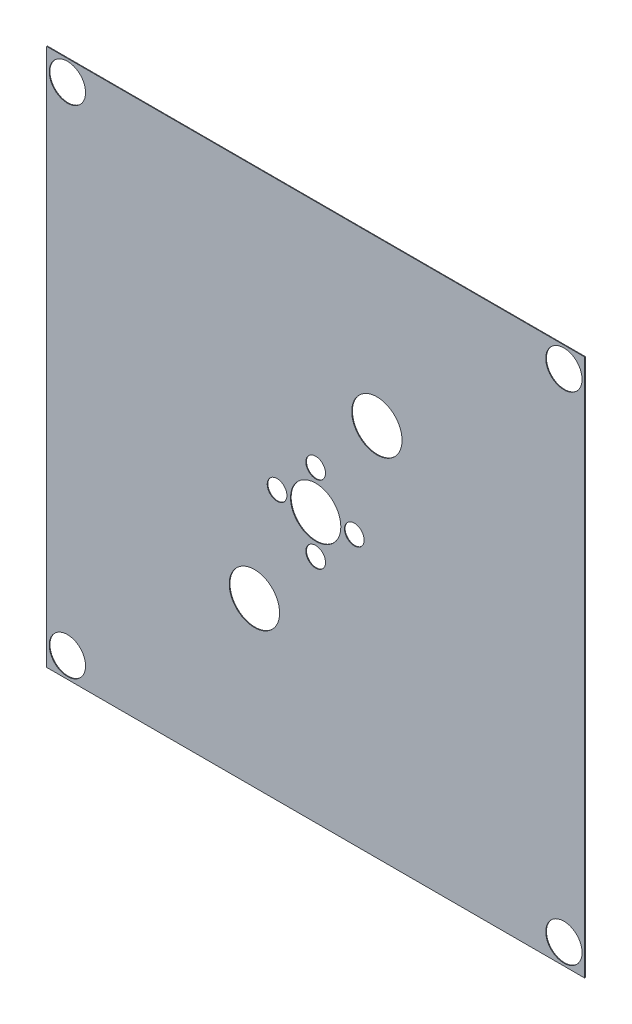
SolidWorks part; units mm, degrees
ref_plane "Front" through (0, 0, 0) normal (0, 0, 1) x (1, 0, 0)
ref_plane "Top" through (0, 0, 0) normal (0, 1, 0) x (1, 0, 0)
ref_plane "Right" through (0, 0, 0) normal (1, 0, 0) x (0, 0, -1)
sketch "Sketch1" plane through (0, 0, 0) normal (0, 0, 1) x (1, 0, 0)
  line L1 (-975, 975) -> (975, 975)
  line L2 (-975, 975) -> (-975, -975)
  line L3 (-975, -975) -> (975, -975)
  line L4 (975, 975) -> (975, -975)
  line L5 (-975, 975) -> (975, -975) construction
  line L6 (-975, -975) -> (975, 975) construction
  point P0 (0, 0)
  dimension "D1" = 1950
  dimension "D2" = 1950
extrude "Boss-Extrude1" add sketch "Sketch1" along normal blind 2.4
sketch "Sketch2" plane through (0, 0, 2.4) normal (0, 0, 1) x (1, 0, 0)
  line L0 (-975, 0) -> (975, 0) construction
  line L1 (-975, 975) -> (-975, -975) construction
  line L2 (975, -975) -> (975, 975) construction
  line L3 (0, 975) -> (0, -975) construction
  line L4 (975, 975) -> (-975, 975) construction
  line L5 (-975, -975) -> (975, -975) construction
  line L6 (-975, 975) -> (0, 0) construction
  circle A0 centre (0, 0) radius 91.2
  circle A1 centre (0, 140) radius 35.65
  circle A3 centre (222, 382) radius 91.2
  circle A4 centre (-222, -382) radius 91.2
  circle A5 centre (-900, 900) radius 65.8
  circle A6 centre (-900, -900) radius 65.8
  circle A7 centre (0, -140) radius 35.65
  circle A8 centre (900, 900) radius 65.8
  circle A9 centre (140, 0) radius 35.65
  circle A10 centre (-140, 0) radius 35.65
  circle A11 centre (900, -900) radius 65.8
  dimension "D1" = 182.4
  dimension "D3" = 71.3
  dimension "D4" = 182.4
  dimension "D7" = 182.4
  dimension "D10" = 131.6
  dimension "D2" = 140
  dimension "D5" = 222
  dimension "D6" = 382
  dimension "D8" = 222
  dimension "D9" = 382
  dimension "D11" = 900
extrude "Cut-Extrude1" cut sketch "Sketch2" against normal through all
